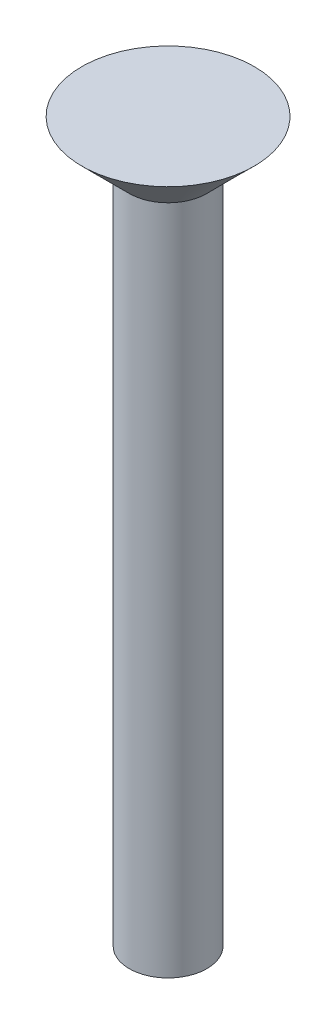
SolidWorks part; units mm, degrees
ref_plane "Front Plane" through (0, 0, 0) normal (0, 0, 1) x (1, 0, 0)
ref_plane "Top Plane" through (0, 0, 0) normal (0, 1, 0) x (1, 0, 0)
ref_plane "Right Plane" through (0, 0, 0) normal (1, 0, 0) x (0, 0, -1)
other "Default"
sketch "Threads" plane through (0, 0, 0) normal (0, 0, 1) x (1, 0, 0)
  line L0 (0, -11.675) -> (0, 11.675)
  line L1 (0, 11.675) -> (1.35, 11.675)
  line L2 (1.35, 11.675) -> (1.35, -11.675)
  line L3 (1.35, -11.675) -> (0, -11.675)
  line L4 (0, -5.7066) -> (0, 6.3425) construction
  dimension "Length" = 23.35
  dimension "Diameter" = 2.7
revolve "Revolve1" add sketch "Threads" angle 360 about L4
ref_plane "Head Top" through (0, 13.325, 0) normal (0, 1, 0) x (1, 0, 0)
sketch "Head" plane through (0, 13.325, 0) normal (0, 1, 0) x (1, 0, 0)
  circle A0 centre (0, 0) radius 3
  dimension "Diameter" = 6
sketch "Sketch5" plane through (0, 0, 0) normal (0, 0, 1) x (1, 0, 0)
  line L0 (3, 13.325) -> (-3, 13.325) construction
  line L1 (3, 13.325) -> (-3, 13.325) construction
  line L2 (0, -1.1215) -> (0, 5.6187) construction
  line L3 (0, 13.325) -> (0, 11.675)
  line L4 (0, 11.675) -> (1.35, 11.675)
  line L5 (1.35, 11.675) -> (3, 13.325)
  line L6 (3, 13.325) -> (0, 13.325)
revolve "Flat" add sketch "Sketch5" angle 360 about L2
